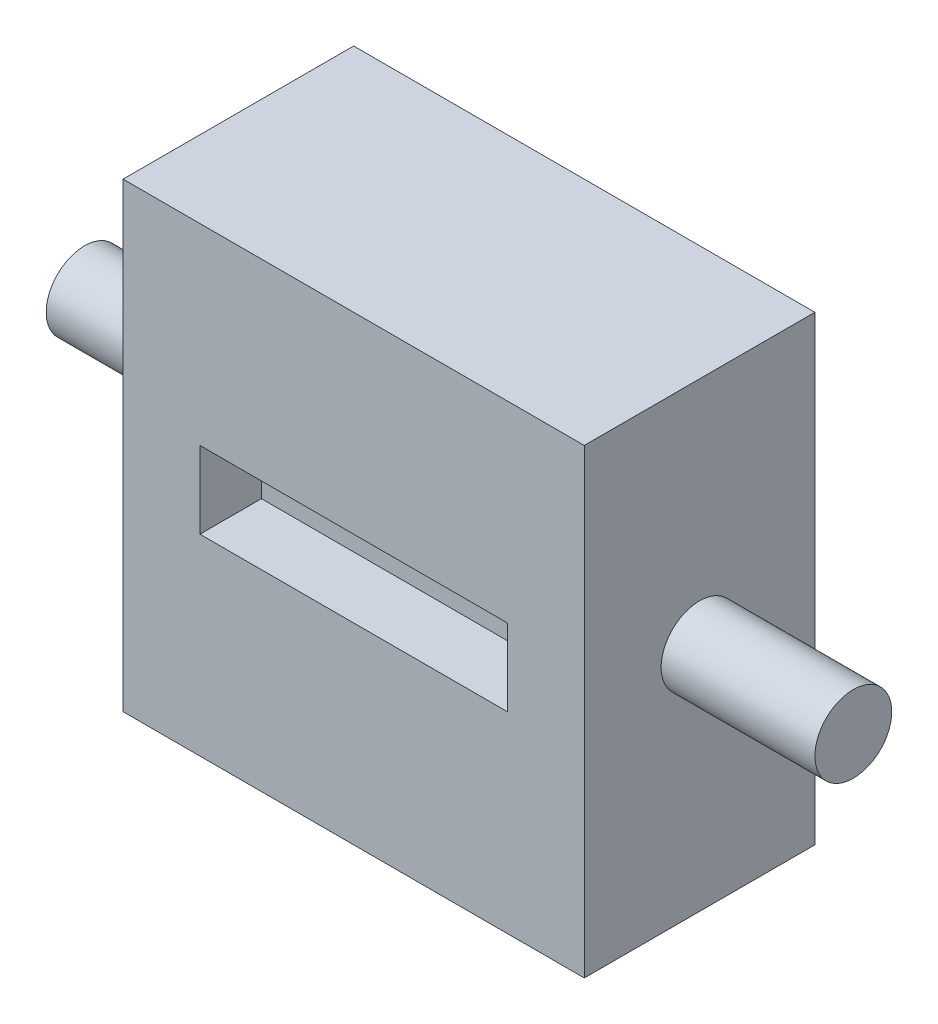
SolidWorks part; units mm, degrees
ref_plane "Front Plane" through (0, 0, 0) normal (0, 0, 1) x (1, 0, 0)
ref_plane "Top Plane" through (0, 0, 0) normal (0, 1, 0) x (1, 0, 0)
ref_plane "Right Plane" through (0, 0, 0) normal (1, 0, 0) x (0, 0, -1)
sketch "Sketch1" plane through (0, 0, 0) normal (0, 0, 1) x (1, 0, 0)
  line L1 (-19.05, -19.05) -> (19.05, -19.05)
  line L2 (-19.05, -19.05) -> (-19.05, 19.05)
  line L3 (-19.05, 19.05) -> (19.05, 19.05)
  line L4 (19.05, -19.05) -> (19.05, 19.05)
  line L5 (-19.05, -19.05) -> (19.05, 19.05) construction
  line L6 (-19.05, 19.05) -> (19.05, -19.05) construction
  point P0 (0, 0)
  dimension "D1" = 38.1
  dimension "D2" = 38.1
extrude "Boss-Extrude1" add sketch "Sketch1" along normal mid plane 19.05
sketch "Sketch2" plane through (0, 0, 9.525) normal (0, 0, 1) x (1, 0, 0)
  line L11 (-12.7, 3.175) -> (12.7, 3.175)
  line L12 (-12.7, 3.175) -> (-12.7, -3.175)
  line L13 (-12.7, -3.175) -> (12.7, -3.175)
  line L14 (12.7, 3.175) -> (12.7, -3.175)
  line L15 (-12.7, 3.175) -> (12.7, -3.175) construction
  line L16 (-12.7, -3.175) -> (12.7, 3.175) construction
  point P0 (0, 0)
  dimension "D1" = 6.35
  dimension "D2" = 25.4
extrude "Cut-Extrude1" cut sketch "Sketch2" against normal blind 5.08
sketch "Sketch3" plane through (0, 0, -9.525) normal (0, 0, -1) x (-1, 0, 0)
  line L0 (3.175, 3.175) -> (9.525, 3.175)
  line L1 (-3.175, 9.525) -> (3.175, 9.525)
  line L2 (-3.175, 9.525) -> (-3.175, 3.175)
  line L3 (-3.175, -9.525) -> (3.175, -9.525)
  line L4 (3.175, 9.525) -> (3.175, 3.175)
  line L5 (-9.525, 3.175) -> (-3.175, 3.175)
  line L6 (-9.525, 3.175) -> (-9.525, -3.175)
  line L7 (-9.525, -3.175) -> (-3.175, -3.175)
  line L8 (9.525, 3.175) -> (9.525, -3.175)
  line L9 (-3.175, -3.175) -> (-3.175, -9.525)
  line L10 (3.175, -3.175) -> (9.525, -3.175)
  line L11 (3.175, -3.175) -> (3.175, -9.525)
  dimension "D1" = 6.35
  dimension "D2" = 6.35
  dimension "D3" = 19.05
  dimension "D4" = 19.05
  dimension "D5" = 9.525
  dimension "D6" = 9.525
  dimension "D7" = 3.175
  dimension "D8" = 3.175
extrude "Cut-Extrude2" cut sketch "Sketch3" against normal blind 5.08
sketch "Sketch4" plane through (19.05, 0, 0) normal (1, 0, 0) x (0, 0, -1)
  line L0 (-9.525, -19.05) -> (9.525, -19.05) construction
  circle A0 centre (0, 0) radius 3.175
  dimension "D1" = 6.35
  dimension "D2" = 0
  dimension "D3" = 19.05
extrude "Boss-Extrude2" add sketch "Sketch4" along normal blind 12.7
mirror "Mirror1" about plane through (0, 0, 0) normal (1, 0, 0) of "Boss-Extrude2"
